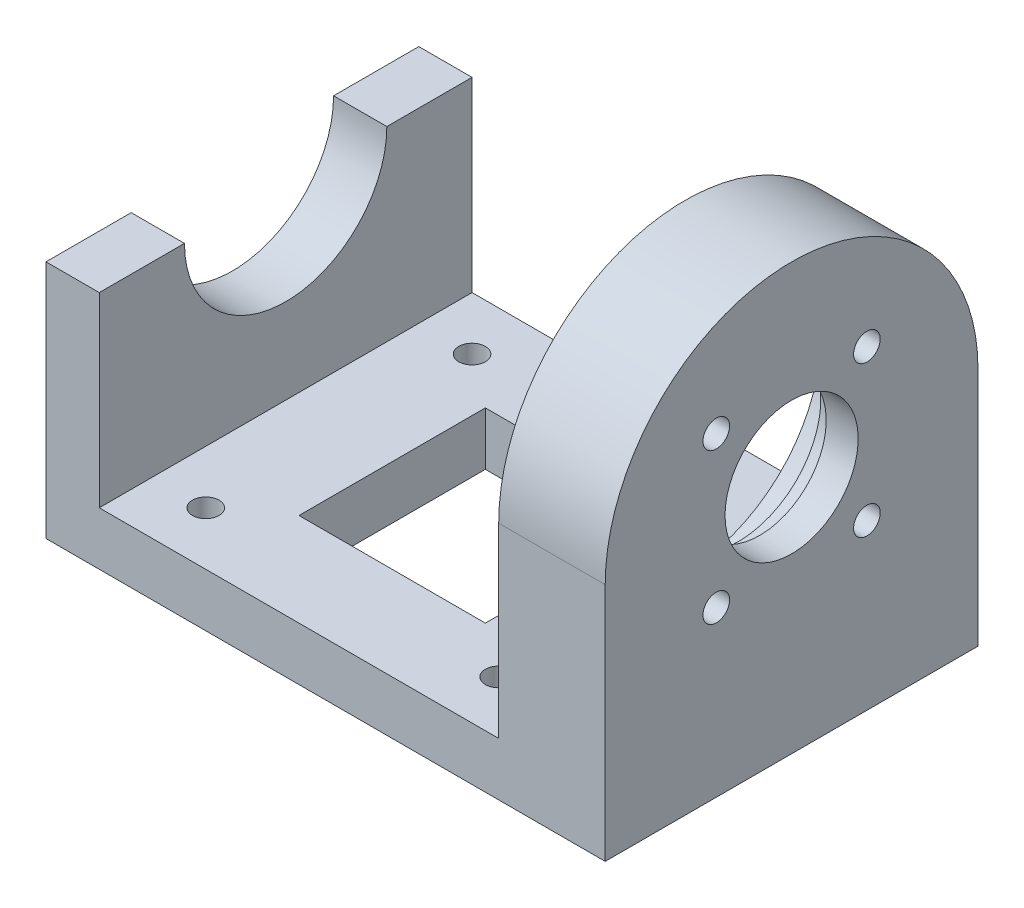
SolidWorks part; units mm, degrees
material "ABS"
ref_plane "Front Plane" through (0, 0, 0) normal (0, 0, 1) x (1, 0, 0)
ref_plane "Top Plane" through (0, 0, 0) normal (0, 1, 0) x (1, 0, 0)
ref_plane "Right Plane" through (0, 0, 0) normal (1, 0, 0) x (0, 0, -1)
sketch "Sketch1" plane through (0, 0, 0) normal (0, 1, 0) x (1, 0, 0)
  line L1 (-52.5, -35) -> (52.5, -35)
  line L2 (-52.5, -35) -> (-52.5, 35)
  line L3 (-52.5, 35) -> (52.5, 35)
  line L4 (52.5, -35) -> (52.5, 35)
  line L5 (-52.5, -35) -> (52.5, 35) construction
  line L6 (-52.5, 35) -> (52.5, -35) construction
  point P0 (0, 0)
  dimension "D1" = 70
  dimension "D2" = 105
extrude "Boss-Extrude1" add sketch "Sketch1" along normal blind 10
sketch "Sketch2" plane through (0, 10, 0) normal (0, 1, 0) x (1, 0, 0)
  line L0 (-52.5, -35) -> (52.5, -35) construction
  line L1 (52.5, 35) -> (32.5, 35)
  line L2 (52.5, 35) -> (52.5, -35)
  line L3 (52.5, -35) -> (32.5, -35)
  line L4 (32.5, 35) -> (32.5, -35)
  dimension "D1" = 20
extrude "Boss-Extrude2" add sketch "Sketch2" along normal blind 70
sketch "Sketch3" plane through (32.5, 0, 0) normal (-1, 0, 0) x (0, 0, 1)
  line L0 (-35, 80) -> (-35, 10) construction
  line L1 (-35, 80) -> (-35, 45)
  line L2 (35, 80) -> (35, 10) construction
  line L3 (35, 80) -> (35, 45)
  line L4 (0, 29.9331) -> (0, 64.3237) construction
  line L5 (-25.6841, 45) -> (12.1891, 45) construction
  line L6 (-35, 80) -> (35, 80) construction
  line L7 (-35, 80) -> (35, 80)
  arc A0 (35, 45) -> (-35, 45) centre (0, 45) ccw
  line M6 (35, 10) -> (35, 80)
  line M7 (35, 80) -> (-35, 80)
  line M8 (-35, 80) -> (-35, 10)
  dimension "D1" = 70
extrude "Cut-Extrude1" cut sketch "Sketch3" against normal blind 20 contours A0 L7 M8 | A0 M6 M7
sketch "Sketch4" plane through (32.5, 0, 0) normal (-1, 0, 0) x (0, 0, 1)
  circle A0 centre (0, 45) radius 25.5
  dimension "D1" = 51
extrude "Cut-Extrude2" cut sketch "Sketch4" against normal blind 10
sketch "Sketch5" plane through (42.5, 0, 0) normal (-1, 0, 0) x (0, 0, 1)
  circle A0 centre (0, 45) radius 15.5
  dimension "D1" = 31
extrude "Cut-Extrude3" cut sketch "Sketch5" against normal blind 4
sketch "Sketch6" plane through (46.5, 0, 0) normal (-1, 0, 0) x (0, 0, 1)
  circle A0 centre (0, 45) radius 12.5
  dimension "D1" = 25
sketch "Sketch7" plane through (42.5, 0, 0) normal (-1, 0, 0) x (0, 0, 1)
  line L0 (0, 45) -> (0, 75.751) construction
  line L1 (0, 45) -> (21.9242, 66.9242) construction
  circle A0 centre (0, 45) radius 20 construction
  circle A1 centre (14.1421, 59.1421) radius 2.5
  circle A2 centre (14.1421, 30.8579) radius 2.5
  circle A3 centre (-14.1421, 30.8579) radius 2.5
  circle A4 centre (-14.1421, 59.1421) radius 2.5
  point P17 (0, 45)
  dimension "D1" = 40
  dimension "D2" = 45
  dimension "D3" = 5
  dimension "D4" = 4
extrude "Cut-Extrude5" cut sketch "Sketch7" against normal up to surface (10 mm away) up to face at (52.5, 31.25, 0)
sketch "Sketch9" plane through (0, 10, 0) normal (0, 1, 0) x (1, 0, 0)
  line L0 (-52.5, -35) -> (32.5, -35) construction
  line L1 (-52.5, 35) -> (-42.5, 35)
  line L2 (-52.5, 35) -> (-52.5, -35)
  line L3 (-52.5, -35) -> (-42.5, -35)
  line L4 (-42.5, 35) -> (-42.5, -35)
  dimension "D1" = 10
extrude "Boss-Extrude4" add sketch "Sketch9" along normal blind 35
sketch "Sketch10" plane through (-52.5, 0, 0) normal (-1, 0, 0) x (0, 0, 1)
  line L0 (-35, 0) -> (35, 0) construction
  circle A0 centre (0, 45) radius 19
  dimension "D1" = 38
extrude "Cut-Extrude7" cut sketch "Sketch10" against normal blind 10
sketch "Sketch11" plane through (0, 10, 0) normal (0, 1, 0) x (1, 0, 0)
  line L0 (-32.5, 30.9607) -> (-32.5, -29.6362) construction
  line L1 (-38.3008, 25) -> (26.1593, 25) construction
  line L2 (22.5, 33.7202) -> (22.5, -30.5192) construction
  line L3 (-39.2942, -25) -> (27.815, -25) construction
  line L4 (-42.5, -35) -> (-42.5, 35) construction
  line L5 (32.5, 35) -> (32.5, -35) construction
  line L6 (32.5, 35) -> (-42.5, 35) construction
  line L7 (-42.5, -35) -> (32.5, -35) construction
  circle A0 centre (-32.5, 25) radius 2.5
  circle A1 centre (22.5, 25) radius 2.5
  circle A2 centre (22.5, -25) radius 2.5
  circle A3 centre (-32.5, -25) radius 2.5
  dimension "D5" = 5
  dimension "D6" = 5
  dimension "D7" = 5
  dimension "D8" = 5
  dimension "D1" = 10
  dimension "D2" = 10
  dimension "D3" = 10
  dimension "D4" = 10
extrude "Cut-Extrude9" cut sketch "Sketch11" against normal blind 10
extrude "Cut-Extrude10" cut sketch "Sketch6" against normal blind 10
sketch "Sketch13" plane through (0, 10, 0) normal (0, 1, 0) x (1, 0, 0)
  line L1 (-22.5, -17.5) -> (12.5, -17.5)
  line L2 (-22.5, -17.5) -> (-22.5, 17.5)
  line L3 (-22.5, 17.5) -> (12.5, 17.5)
  line L4 (12.5, -17.5) -> (12.5, 17.5)
  line L5 (-22.5, -17.5) -> (12.5, 17.5) construction
  line L6 (-22.5, 17.5) -> (12.5, -17.5) construction
  line L7 (32.5, 35) -> (-42.5, 35) construction
  line L9 (-42.5, -35) -> (-42.5, 35) construction
  point P0 (-5, 0)
  dimension "D1" = 35
  dimension "D2" = 37.5
  dimension "D3" = 35
  dimension "D4" = 35
extrude "Cut-Extrude11" cut sketch "Sketch13" against normal blind 10
